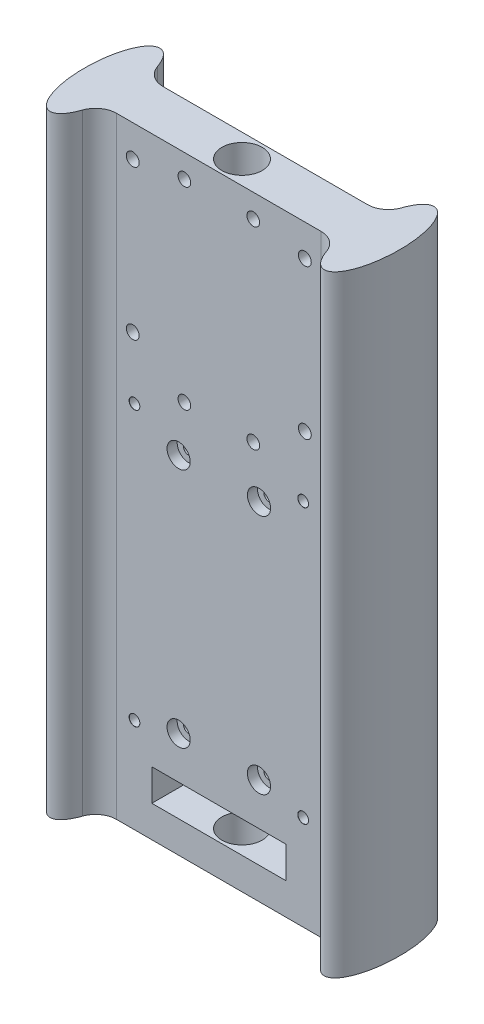
SolidWorks part; units mm, degrees
ref_plane "Front Plane" through (0, 0, 0) normal (0, 0, 1) x (1, 0, 0)
ref_plane "Top Plane" through (0, 0, 0) normal (0, 1, 0) x (1, 0, 0)
ref_plane "Right Plane" through (0, 0, 0) normal (1, 0, 0) x (0, 0, -1)
sketch "Sketch1" plane through (0, 0, 0) normal (0, 1, 0) x (1, 0, 0)
  line L0 (-32.5, 0) -> (-37.35, 0) construction
  line L1 (32.5, 5.5) -> (-32.5, 5.5)
  line L2 (32.5, 5.5) -> (32.5, -5.5)
  line L3 (32.5, -5.5) -> (-32.5, -5.5)
  line L4 (-32.5, 5.5) -> (-32.5, -5.5)
  line L5 (32.5, 5.5) -> (-32.5, -5.5) construction
  line L6 (32.5, -5.5) -> (-32.5, 5.5) construction
  line L7 (32.5, 0) -> (37.35, 0) construction
  circle A0 centre (0, 0) radius 4.7775
  ellipse E0 centre (-32.5, 0) end of major axis (-32.5, -13) minor radius 4.85
  ellipse E1 centre (32.5, 0) end of major axis (32.5, 13) minor radius 4.85
  point P0 (0, 0)
  dimension "D3" = 9.555
  dimension "D1" = 74.7
  dimension "D2" = 11
  dimension "D4" = 65
  dimension "D6" = 13
  dimension "D7" = 13
extrude "Boss-Extrude1" add sketch "Sketch1" along normal blind 145 contours E1 L1 E0 L3 | L3 E0 L1 L4 | L1 E0 L3 L4 | L1 E1 L3 L2 | L3 E1 L1 L2
fillet "Fillet1" radius 5 4 edges at (-28.1054, 72.5, -5.5) (28.1054, 72.5, -5.5) (28.1054, 72.5, 5.5) (-28.1054, 72.5, 5.5)
sketch "Sketch3" plane through (0, 0, -5.5) normal (0, 0, -1) x (-1, 0, 0)
  line L0 (0, 61.275) -> (0, 0) construction
  line L1 (15.875, 20) -> (-15.875, 20)
  line L2 (15.875, 20) -> (15.875, 102.55)
  line L3 (15.875, 102.55) -> (-15.875, 102.55)
  line L4 (-15.875, 20) -> (-15.875, 102.55)
  line L5 (15.875, 20) -> (-15.875, 102.55) construction
  line L6 (15.875, 102.55) -> (-15.875, 20) construction
  line L7 (24.2275, 0) -> (28.9506, 0) construction
  line L8 (-24.2275, 0) -> (24.2275, 0) construction
  line L9 (20.875, 102.55) -> (25.875, 102.55)
  line L10 (9.525, 25) -> (-9.525, 25)
  line L11 (9.525, 25) -> (9.525, 82.15)
  line L12 (9.525, 82.15) -> (-9.525, 82.15)
  line L13 (-9.525, 25) -> (-9.525, 82.15)
  line L14 (9.525, 25) -> (-9.525, 82.15) construction
  line L15 (9.525, 82.15) -> (-9.525, 25) construction
  line L16 (20.875, 102.55) -> (20.875, 20)
  line L17 (20.875, 20) -> (25.875, 20)
  line L18 (25.875, 102.55) -> (25.875, 20)
  line L19 (0, 53.575) -> (0, 20) construction
  line L20 (-15.875, 7.5) -> (15.875, 7.5)
  line L21 (-15.875, 7.5) -> (-15.875, 15)
  line L22 (-15.875, 15) -> (15.875, 15)
  line L23 (15.875, 7.5) -> (15.875, 15)
  point P0 (0, 61.275)
  dimension "D1" = 31.75
  dimension "D2" = 82.55
  dimension "D3" = 20
  dimension "D4" = 57.15
  dimension "D5" = 19.05
  dimension "D6" = 5
  dimension "D7" = 5
  dimension "D8" = 82.55
  dimension "D9" = 20
  dimension "D10" = 7.5
  dimension "D11" = 7.5
  dimension "D12" = 5
extrude "Cut-Extrude2" cut sketch "Sketch3" against normal through all both and the other way through all contours L21 L20 L23 L22
hole_wizard "Tap Drill for M3x0.5 Tap1" positions "3DSketch1" profile "Sketch4" hole size "M3x0.5" standard "ANSI Metric" end condition through all
sketch3d "3DSketch1"
  point P0 (9.525, 82.15, -5.5)
  point P3 (-9.525, 82.15, -5.5)
  point P6 (-9.525, 25, -5.5)
  point P9 (9.525, 25, -5.5)
sketch "Sketch4" plane through (9.525, 82.15, -5.5) normal (1, 0, 0) x (0, 1, 0)
  line L0 (0, 0) -> (0, 18.5)
  line L1 (0, 18.5) -> (1.25, 18.5)
  line L2 (1.25, 18.5) -> (1.25, 0)
  line L5 (1.25, 0) -> (0, 0)
  line L11 (0, -6.35) -> (0, 107.95) construction
  dimension "Thru Hole Dia." = 2.5
  dimension "Thru Hole Depth" = 18.5
sketch "Sketch5" plane through (0, 0, 5.5) normal (0, 0, 1) x (1, 0, 0)
  line L0 (-15.875, 15) -> (15.875, 15) construction
  line L1 (17.5, 25) -> (-17.5, 25)
  line L2 (17.5, 25) -> (17.5, 85)
  line L3 (17.5, 85) -> (-17.5, 85)
  line L4 (-17.5, 25) -> (-17.5, 85)
  line L5 (17.5, 25) -> (-17.5, 85) construction
  line L6 (17.5, 85) -> (-17.5, 25) construction
  line L7 (22.6, 19.9) -> (22.6, 90.1)
  line L8 (0, 15) -> (0, 55) construction
  line L9 (22.6, 90.1) -> (-22.6, 90.1)
  line L10 (-22.6, 19.9) -> (-22.6, 90.1)
  line L11 (22.6, 19.9) -> (-22.6, 19.9)
  line L12 (20, 22.5) -> (20, 87.5) construction
  line L13 (20, 87.5) -> (-20, 87.5) construction
  line L14 (-20, 22.5) -> (-20, 87.5) construction
  line L15 (20, 22.5) -> (-20, 22.5) construction
  line L16 (0, 119.75) -> (0, 145) construction
  line L17 (20.4, 137.5) -> (-20.4, 137.5) construction
  line L18 (20.4, 137.5) -> (20.4, 102) construction
  line L19 (20.4, 102) -> (-20.4, 102) construction
  line L20 (-20.4, 137.5) -> (-20.4, 102) construction
  line L21 (20.4, 137.5) -> (-20.4, 102) construction
  line L22 (20.4, 102) -> (-20.4, 137.5) construction
  line L23 (24.2275, 145) -> (-24.2275, 145) construction
  circle A0 centre (-20.4, 137.5) radius 1.525
  circle A1 centre (20.4, 137.5) radius 1.525
  circle A2 centre (20.4, 102) radius 1.525
  circle A3 centre (-20.4, 102) radius 1.525
  point P0 (0, 55)
  point P17 (0, 119.75)
  dimension "D9" = 3.05
  dimension "D1" = 40
  dimension "D2" = 60
  dimension "D3" = 35
  dimension "D6" = 35.5
  dimension "D7" = 40.8
  dimension "D8" = 7.5
  dimension "D4" = 5.1
  dimension "D5" = 2.5
sketch "Sketch6" plane through (0, 0, 5.5) normal (0, 0, 1) x (1, 0, 0)
  circle A0 centre (9.525, 82.15) radius 2.75
  circle A1 centre (-9.525, 82.15) radius 2.75
  circle A2 centre (9.525, 25) radius 2.75
  circle A4 centre (-9.525, 25) radius 2.75
  dimension "D1" = 5.5
  dimension "D2" = 5.5
  dimension "D3" = 5.5
  dimension "D4" = 5.5
extrude "Cut-Extrude4" cut sketch "Sketch6" against normal blind 2.4
sketch "Sketch7" plane through (0, 0, 5.5) normal (0, 0, 1) x (1, 0, 0)
  point P0 (-20, 87.5)
  point P3 (20, 87.5)
  point P6 (20, 22.5)
  point P9 (-20, 22.5)
hole_wizard "Tap Drill for M3 Tap1" positions "Sketch7" profile "Sketch8" hole size "M3" standard "ISO" end condition through all
sketch "Sketch8" plane through (-20, 87.5, 5.5) normal (1, 0, 0) x (0, -1, 0)
  line L0 (0, 0) -> (0, 18.5)
  line L1 (0, 18.5) -> (1.25, 18.5)
  line L2 (1.25, 18.5) -> (1.25, 0.025)
  line L3 (1.25, 0.025) -> (1.275, 0)
  line L5 (1.275, 0) -> (0, 0)
  line L6 (-1.25, 0.025) -> (-1.275, 0) construction
  line L11 (0, -6.35) -> (0, 107.95) construction
  dimension "Thru Hole Dia." = 2.5
  dimension "Thru Hole Depth" = 18.5
  dimension "Near C'Sink Dia." = 2.55
  dimension "Near C'Sink Angle" = 90
sketch "Sketch9" plane through (0, 0, -5.5) normal (0, 0, -1) x (-1, 0, 0)
  line L0 (0, 0) -> (0, 145) construction
  line L1 (-24.2275, 0) -> (24.2275, 0) construction
  line L2 (-24.2275, 145) -> (24.2275, 145) construction
  line L3 (0, 116.6) -> (-10.668, 116.6) construction
  line L4 (10.668, 142) -> (-10.668, 142)
  line L5 (10.668, 142) -> (10.668, 91.2)
  line L6 (10.668, 91.2) -> (-10.668, 91.2)
  line L7 (-10.668, 142) -> (-10.668, 91.2)
  line L8 (10.668, 142) -> (-10.668, 91.2) construction
  line L9 (10.668, 91.2) -> (-10.668, 142) construction
  circle A0 centre (-8.168, 139.5) radius 1.5
  circle A1 centre (-8.168, 93.7) radius 1.5
  circle A2 centre (8.168, 93.7) radius 1.5
  circle A3 centre (8.168, 139.5) radius 1.5
  point P6 (0, 116.6)
  dimension "D4" = 3
  dimension "D6" = 2.5
  dimension "D1" = 21.336
  dimension "D2" = 50.8
  dimension "D3" = 3
  dimension "D5" = 2.5
extrude "Cut-Extrude5" cut sketch "Sketch9" against normal through all contours A0 | A3 | A2 | A1
extrude "Cut-Extrude6" cut sketch "Sketch5" against normal up to next contours A2 | A3 | A1 | A0
